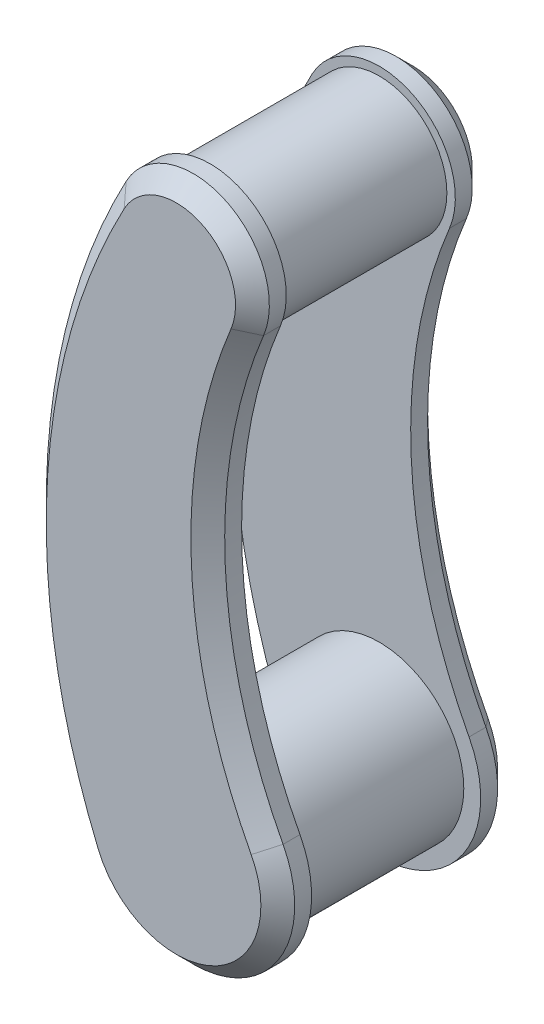
SolidWorks part; units mm, degrees
ref_plane "Front Plane" through (0, 0, 0) normal (0, 0, 1) x (1, 0, 0)
ref_plane "Top Plane" through (0, 0, 0) normal (0, 1, 0) x (1, 0, 0)
ref_plane "Right Plane" through (0, 0, 0) normal (1, 0, 0) x (0, 0, -1)
ref_plane "Plane1" through (0, 0, 25) normal (0, 0, 1) x (1, 0, 0)
sketch "Sketch2" plane through (0, 0, 25) normal (0, 0, 1) x (1, 0, 0)
  line L0 (0, 75) -> (0, -75) construction
  arc A0 (20.7778, 66.3668) -> (-19.8422, 85.6083) centre (0, 75) ccw
  arc A1 (-27.6235, -86.7022) -> (26.5495, -61.0312) centre (0, -75) ccw
  arc A2 (-19.8422, 85.6083) -> (-27.6235, -86.7022) centre (156.5332, -8.6875) ccw
  arc A3 (20.7778, 66.3668) -> (26.5495, -61.0312) centre (159.2968, 8.8125) ccw
  point P10 (0, 0)
  dimension "D1" = 45
  dimension "D2" = 60
  dimension "D4" = 200
  dimension "D5" = 150
  dimension "D3" = 150
extrude "Boss-Extrude1" add sketch "Sketch2" along normal blind 10
chamfer "Chamfer2" distance 5 angle 45 4 edges at (9.6321, 95.334, 35) (-43.2632, 0.335, 35) (9.4505, 2.0239, 35) (12.8467, -102.1102, 35)
sketch "Sketch4" plane through (0, 0, 25) normal (0, 0, -1) x (-1, 0, 0)
  circle A0 centre (0, 75) radius 20
  circle A1 centre (0, -75) radius 25
  dimension "D1" = 50
  dimension "D2" = 40
extrude "Boss-Extrude2" add sketch "Sketch4" along normal blind 30
mirror "Mirror3" about plane through (0, 0, 0) normal (0, 0, 1) of bodies 102
